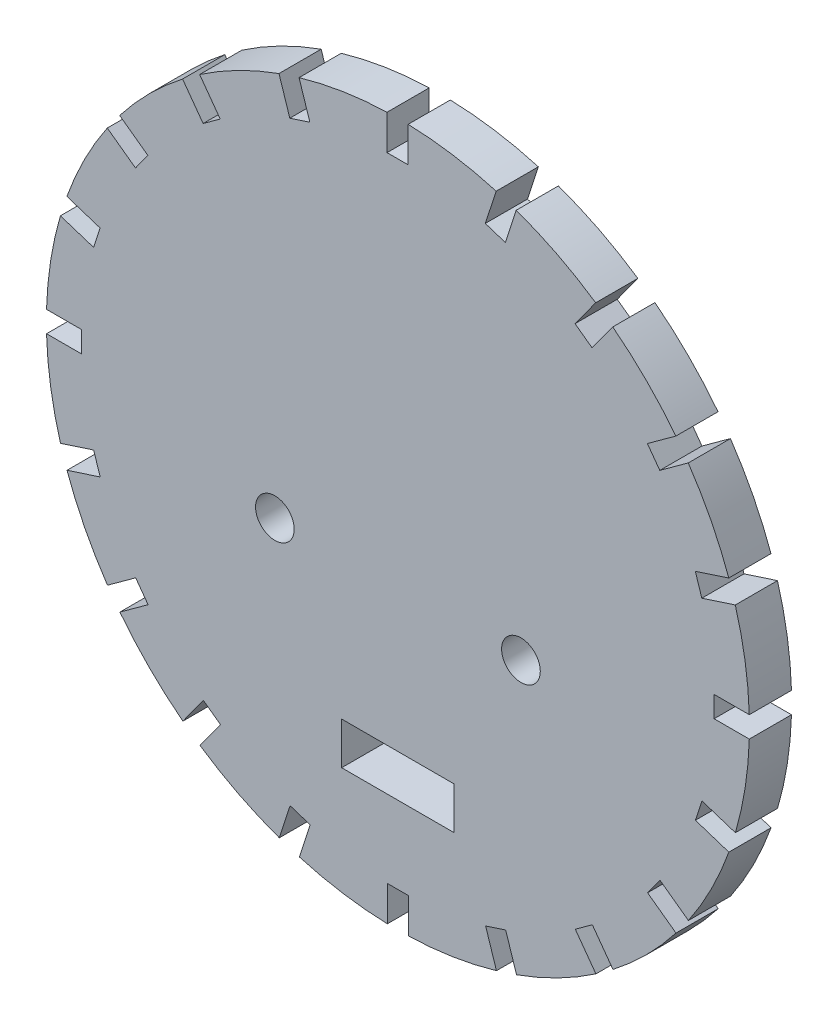
SolidWorks part; units mm, degrees
ref_plane "Front Plane" through (0, 0, 0) normal (0, 0, 1) x (1, 0, 0)
ref_plane "Top Plane" through (0, 0, 0) normal (0, 1, 0) x (1, 0, 0)
ref_plane "Right Plane" through (0, 0, 0) normal (1, 0, 0) x (0, 0, -1)
sketch "Sketch2" plane through (0, 0, 0) normal (0, 0, 1) x (1, 0, 0)
  line L0 (-155.1279, 0) -> (168.9897, -1.4796) construction
  line L1 (0, 103.9637) -> (0, -102.4062) construction
  line L2 (-1.5, -50.6857) -> (-1.5, -45.7082)
  line L3 (-1.5, -45.7082) -> (1.5, -45.7082)
  line L4 (1.5, -45.7082) -> (1.5, -50.6857)
  line L5 (-16.8703, -47.7835) -> (-15.3322, -43.0496)
  line L6 (-8, -28.7082) -> (8, -28.7082)
  line L7 (-8, -28.7082) -> (-8, -34.7082)
  line L8 (-8, -34.7082) -> (8, -34.7082)
  line L9 (8, -28.7082) -> (8, -34.7082)
  line L10 (-15.3322, -43.0496) -> (-12.479, -43.9767)
  line L11 (-12.479, -43.9767) -> (-14.0171, -48.7106)
  line L12 (-30.5915, -40.2737) -> (-27.6658, -36.2468)
  line L13 (-27.6658, -36.2468) -> (-25.2388, -38.0102)
  line L14 (-25.2388, -38.0102) -> (-28.1645, -42.037)
  line L15 (-41.3205, -28.8913) -> (-37.2937, -25.9656)
  line L16 (-37.2937, -25.9656) -> (-35.5303, -28.3927)
  line L17 (-35.5303, -28.3927) -> (-39.5572, -31.3184)
  line L18 (-48.0071, -14.7506) -> (-43.2732, -13.2125)
  line L19 (-43.2732, -13.2125) -> (-42.3462, -16.0657)
  line L20 (-42.3462, -16.0657) -> (-47.08, -17.6038)
  line L21 (-49.9967, 0.7642) -> (-45.0192, 0.7642)
  line L22 (-45.0192, 0.7642) -> (-45.0192, -2.2358)
  line L23 (-45.0192, -2.2358) -> (-49.9967, -2.2358)
  line L24 (-47.0945, 16.1345) -> (-42.3606, 14.5964)
  line L25 (-42.3606, 14.5964) -> (-43.2877, 11.7432)
  line L26 (-43.2877, 11.7432) -> (-48.0215, 13.2814)
  line L27 (-39.5847, 29.8558) -> (-35.5578, 26.9301)
  line L28 (-35.5578, 26.9301) -> (-37.3211, 24.503)
  line L29 (-37.3211, 24.503) -> (-41.348, 27.4287)
  line L30 (-28.2023, 40.5848) -> (-25.2766, 36.5579)
  line L31 (-25.2766, 36.5579) -> (-27.7037, 34.7945)
  line L32 (-27.7037, 34.7945) -> (-30.6294, 38.8214)
  line L33 (-14.0616, 47.2713) -> (-12.5235, 42.5374)
  line L34 (-12.5235, 42.5374) -> (-15.3767, 41.6104)
  line L35 (-15.3767, 41.6104) -> (-16.9148, 46.3443)
  line L36 (1.4532, 49.2707) -> (1.4532, 44.2834)
  line L37 (1.4532, 44.2834) -> (-1.5468, 44.2834)
  line L38 (-1.5468, 44.2834) -> (-1.5468, 49.2609)
  line L39 (16.8287, 46.3747) -> (15.2854, 41.6248)
  line L40 (15.2854, 41.6248) -> (12.4323, 42.5519)
  line L41 (12.4323, 42.5519) -> (13.9748, 47.2992)
  line L42 (30.558, 38.8671) -> (27.6191, 34.822)
  line L43 (27.6191, 34.822) -> (25.192, 36.5854)
  line L44 (25.192, 36.5854) -> (28.1296, 40.6286)
  line L45 (41.2953, 27.4822) -> (37.2469, 24.5408)
  line L46 (37.2469, 24.5408) -> (35.4836, 26.9679)
  line L47 (35.4836, 26.9679) -> (39.5303, 29.908)
  line L48 (47.9875, 13.3347) -> (43.2264, 11.7877)
  line L49 (43.2264, 11.7877) -> (42.2994, 14.6409)
  line L50 (42.2994, 14.6409) -> (47.0589, 16.1873)
  line L51 (49.9781, -2.189) -> (44.9724, -2.189)
  line L52 (44.9724, -2.189) -> (44.9724, 0.811)
  line L53 (44.9724, 0.811) -> (49.9769, 0.811)
  line L54 (47.072, -17.5672) -> (42.3138, -16.0212)
  line L55 (42.3138, -16.0212) -> (43.2409, -13.168)
  line L56 (43.2409, -13.168) -> (47.9984, -14.7138)
  line L57 (39.5548, -31.2928) -> (35.511, -28.3549)
  line L58 (35.511, -28.3549) -> (37.2744, -25.9278)
  line L59 (37.2744, -25.9278) -> (41.3178, -28.8655)
  line L60 (28.1641, -42.0214) -> (25.2299, -37.9827)
  line L61 (25.2299, -37.9827) -> (27.6569, -36.2193)
  line L62 (27.6569, -36.2193) -> (30.5911, -40.2579)
  line L63 (14.0172, -48.7032) -> (12.4767, -43.9622)
  line L64 (12.4767, -43.9622) -> (15.3299, -43.0352)
  line L65 (15.3299, -43.0352) -> (16.8703, -47.7761)
  arc A0 (1.5, -50.6857) -> (14.0172, -48.7032) centre (0, -0.7082) ccw
  circle A1 centre (-17.5, -8.7082) radius 2.75
  circle A2 centre (-17.5, -8.7082) radius 5.25
  circle A3 centre (17.5, -8.7082) radius 5.25
  circle A4 centre (17.5, -8.7082) radius 2.75
  arc A5 (-30.625, 38.8154) -> (-39.5758, 29.8493) centre (0, -0.7082) ccw
  arc A6 (-16.9147, 46.3439) -> (-28.1995, 40.5809) centre (0, -0.7082) ccw
  arc A7 (-14.015, -48.7038) -> (-1.5, -50.6857) centre (0, -0.7082) ccw
  arc A8 (-28.1568, -42.0264) -> (-16.8682, -47.7769) centre (0, -0.7082) ccw
  arc A9 (-39.543, -31.3081) -> (-30.5841, -40.2634) centre (0, -0.7082) ccw
  arc A10 (-47.0611, -17.5977) -> (-41.307, -28.8815) centre (0, -0.7082) ccw
  arc A11 (-49.9767, -2.2358) -> (-47.9893, -14.7449) centre (0, -0.7082) ccw
  arc A12 (-48.0046, 13.2759) -> (-49.9783, 0.7642) centre (0, -0.7082) ccw
  arc A13 (-41.3371, 27.4208) -> (-47.0796, 16.1297) centre (0, -0.7082) ccw
  arc A14 (16.8703, -47.7761) -> (28.1641, -42.0214) centre (0, -0.7082) ccw
  arc A15 (30.5911, -40.2579) -> (39.5548, -31.2928) centre (0, -0.7082) ccw
  arc A16 (41.3178, -28.8655) -> (47.072, -17.5672) centre (0, -0.7082) ccw
  arc A17 (47.9984, -14.7138) -> (49.9781, -2.189) centre (0, -0.7082) ccw
  arc A18 (49.9769, 0.811) -> (47.9875, 13.3347) centre (0, -0.7082) ccw
  arc A19 (47.0589, 16.1873) -> (41.2953, 27.4822) centre (0, -0.7082) ccw
  arc A20 (13.9748, 47.2992) -> (1.4532, 49.2707) centre (0, -0.7082) ccw
  arc A21 (28.1296, 40.6286) -> (16.8287, 46.3747) centre (0, -0.7082) ccw
  arc A22 (39.5303, 29.908) -> (30.558, 38.8671) centre (0, -0.7082) ccw
  arc A23 (-1.5468, 49.2609) -> (-14.0602, 47.2669) centre (0, -0.7082) ccw
  point P5 (0, -0.7082)
  point P18 (0, -8.7082)
  point P101 (-0.0234, -0.7124)
  dimension "D1" = 100
  dimension "D3" = 5.5
  dimension "D10" = 10.5
  dimension "D2" = 8.0798
  dimension "D4" = 17.5
  dimension "D5" = 1.5
  dimension "D6" = 20
  dimension "D7" = 16
  dimension "D8" = 8
  dimension "D9" = 6
  dimension "D11" = 3
  dimension "D12" = 45
  dimension "D13" = 20
extrude "Boss-Extrude1" add sketch "Sketch2" along normal blind 6 contours A1 | A3 A4 | L38 A23 L33 L34 L35 A6 L30 L31 L32 A5 L27 L28 L29 A13 L24 L25 L26 A12 L21 L22 L23 A11 L18 L19 L20 A10 L15 L16 L17 A9 L12 L13 L14 A8 L5 L10 L11 A7 L2 L3 L4 A0 L63 L64 L65 A14 L60 L61 L62 A15 L57 | A2 A1
sketch "Sketch3" plane through (0, 0, 0) normal (0, 0, -1) x (-1, 0, 0)
  circle A0 centre (-17.5, -8.7082) radius 5.25
  circle A1 centre (17.5, -8.7082) radius 5.25
extrude "Cut-Extrude1" cut sketch "Sketch3" against normal blind 1.5
